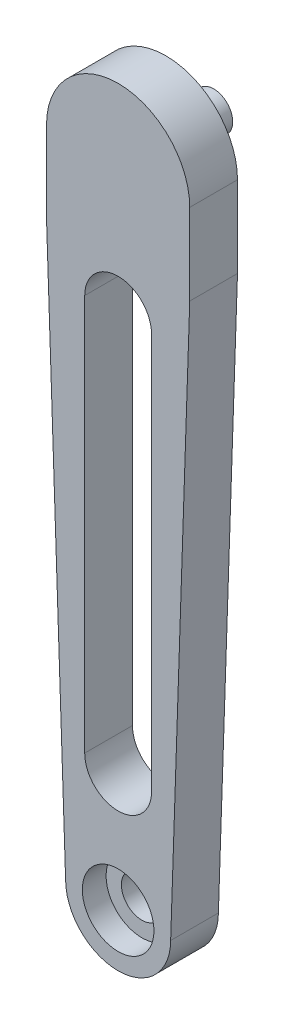
SolidWorks part; units mm, degrees
ref_plane "Front Plane" through (0, 0, 0) normal (0, 0, 1) x (1, 0, 0)
ref_plane "Top Plane" through (0, 0, 0) normal (0, 1, 0) x (1, 0, 0)
ref_plane "Right Plane" through (0, 0, 0) normal (1, 0, 0) x (0, 0, -1)
sketch "Sketch1" plane through (0, 0, 0) normal (0, 0, 1) x (1, 0, 0)
  line L0 (-15, 135) -> (-15, 0)
  line L1 (15, 135) -> (15, 0)
  circle A0 centre (0, 135) radius 7.5
  circle A1 centre (0, 0) radius 7.5
  arc A2 (15, 135) -> (-15, 135) centre (0, 135) ccw
  arc A3 (-15, 0) -> (15, 0) centre (0, 0) ccw
  dimension "D2" = 15
  dimension "D3" = 30
  dimension "D1" = 135
extrude "Boss-Extrude1" add sketch "Sketch1" along normal blind 10
sketch "Sketch2" plane through (0, 0, 0) normal (0, 0, -1) x (-1, 0, 0)
  circle A0 centre (0, 135) radius 7.5 construction
  circle A1 centre (0, 135) radius 7.5
  circle A2 centre (0, 135) radius 4
  dimension "D1" = 8
extrude "Boss-Extrude2" add sketch "Sketch2" against normal up to surface (10 mm away) up to face at (7.5, 135, 10)
sketch "Sketch3" plane through (0, 0, 10) normal (0, 0, 1) x (1, 0, 0)
  circle A0 centre (0, 135) radius 4 construction
  circle A1 centre (0, 135) radius 4
extrude "Boss-Extrude3" add sketch "Sketch3" against normal blind 20
sketch "Sketch5" plane through (0, 0, 10) normal (0, 0, 1) x (1, 0, 0)
  line L0 (-11, 0) -> (-15, 118)
  line L1 (-15, 135) -> (-15, 0) construction
  line L2 (11, 0) -> (15, 118)
  line L3 (15, 0) -> (15, 135) construction
  line L4 (-15, 118) -> (-15, 0)
  line L5 (15, 0) -> (15, 118)
  arc A0 (-11, 0) -> (11, 0) centre (0, 0) ccw
  arc A1 (-15, 0) -> (15, 0) centre (0, 0) ccw construction
  arc A2 (-15, 0) -> (15, 0) centre (0, 0) ccw
  dimension "D1" = 22
  dimension "D2" = 118
extrude "Cut-Extrude2" cut sketch "Sketch5" against normal through all
sketch "Sketch6" plane through (0, 0, 0) normal (0, 0, -1) x (-1, 0, 0)
  circle A0 centre (0, 0) radius 7.5 construction
  circle A1 centre (0, 0) radius 7.5
  circle A2 centre (0, 0) radius 4.3
  dimension "D1" = 3.2
extrude "Boss-Extrude4" add sketch "Sketch6" against normal blind 5.0216
sketch "Sketch7" plane through (0, 0, 0) normal (0, 0, -1) x (-1, 0, 0)
  line L0 (-7, 108) -> (-7, 25)
  line L1 (7, 108) -> (7, 25)
  arc A0 (-7, 25) -> (7, 25) centre (0, 25) ccw
  arc A1 (7, 108) -> (-7, 108) centre (0, 108) ccw
  point P9 (0, 0)
  point P10 (0, 0)
  dimension "D2" = 14
  dimension "D1" = 83
  dimension "D3" = 25
extrude "Cut-Extrude3" cut sketch "Sketch7" against normal up to surface (10 mm away) up to face at (0, 85, 10)
